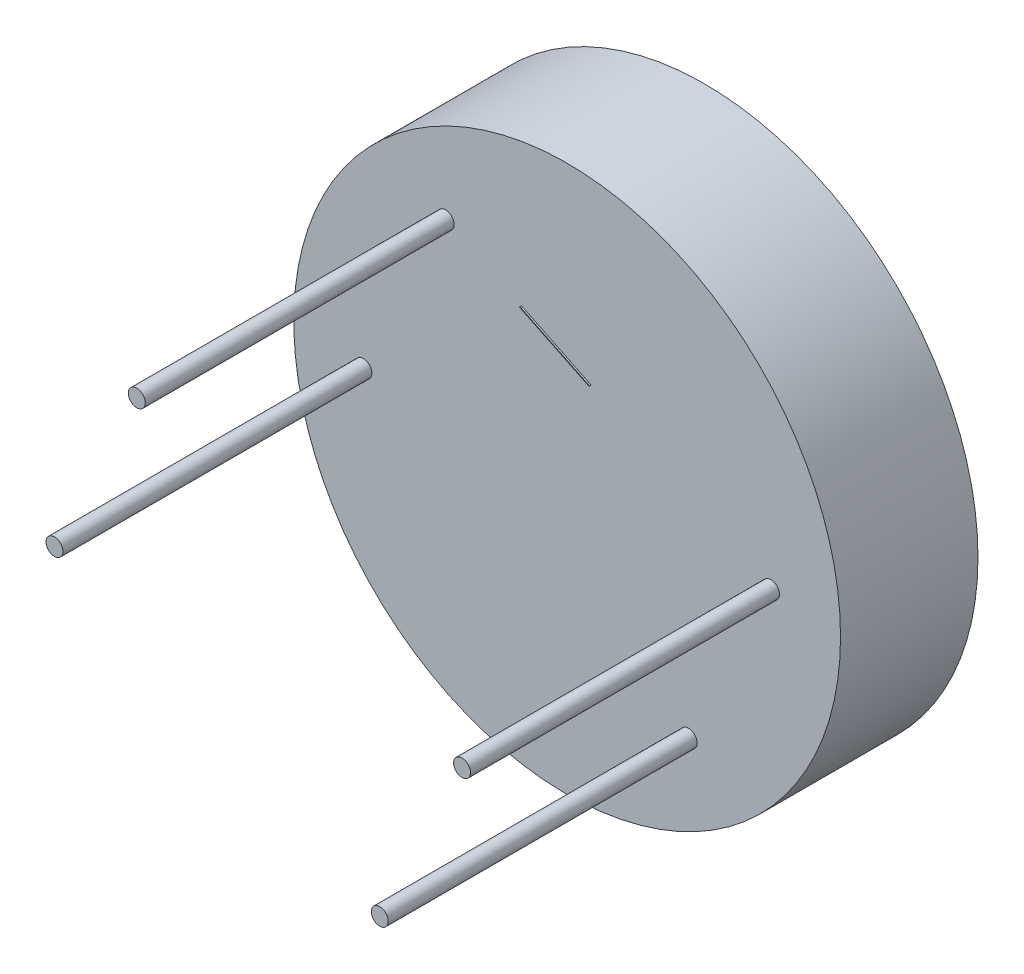
SolidWorks part; units mm, degrees
ref_plane "Plan de face" through (0, 0, 0) normal (0, 0, 1) x (1, 0, 0)
ref_plane "Plan de dessus" through (0, 0, 0) normal (0, 1, 0) x (1, 0, 0)
ref_plane "Plan de droite" through (0, 0, 0) normal (1, 0, 0) x (0, 0, -1)
sketch "Esquisse1" plane through (0, 0, 0) normal (0, 0, 1) x (1, 0, 0)
  circle A0 centre (0, 0) radius 177
  dimension "D1" = 354
extrude "Boss.-Extru.1" add sketch "Esquisse1" along normal blind 89
sketch "Esquisse2" plane through (0, 0, 89) normal (0, 0, 1) x (1, 0, 0)
  circle A0 centre (-131.9397, -3.9883) radius 5.5
  circle A1 centre (78.6481, -106.0117) radius 5.5
  circle A2 centre (131.9397, 3.9883) radius 5.5
  circle A3 centre (-78.6481, 106.0117) radius 5.5
  circle A4 centre (0, 0) radius 177 construction
  dimension "D1" = 11
  dimension "D2" = 11
  dimension "D3" = 11
  dimension "D4" = 11
  dimension "D6" = 132
  dimension "D7" = 132
  dimension "D8" = 132
  dimension "D5" = 132
  dimension "D9" = 234
  dimension "D10" = 110
  dimension "D11" = 234
  dimension "D12" = 110
extrude "Boss.-Extru.2" add sketch "Esquisse2" along normal blind 200
sketch "Esquisse3" [suppressed] plane through (0, 0, 89) normal (0, 0, 1) x (1, 0, 0)
  line L0 (-78.6481, 106.0117) -> (-131.9397, -3.9883) construction
  line L1 (-87.9507, 86.8101) -> (-120.4147, 19.8006)
  line L2 (-120.4147, 19.8006) -> (-119.9648, 19.5826)
  line L3 (-119.9648, 19.5826) -> (-87.5007, 86.5921)
  line L4 (-87.5007, 86.5921) -> (-87.9507, 86.8101)
  dimension "D1" = 0.5
extrude "Boss.-Extru.3" [suppressed] add sketch "Esquisse3" along normal blind 1
sketch "Esquisse4" plane through (0, 0, 89) normal (0, 0, 1) x (1, 0, 0)
  line L0 (-78.6481, 106.0117) -> (131.9397, 3.9883) construction
  line L1 (-29.6405, 82.269) -> (-29.8585, 81.8191)
  line L2 (-29.8585, 81.8191) -> (15.1389, 60.0192)
  line L3 (15.1389, 60.0192) -> (15.3569, 60.4692)
  line L4 (15.3569, 60.4692) -> (-29.6405, 82.269)
  dimension "D1" = 0.5
  dimension "D2" = 50
extrude "Boss.-Extru.4" add sketch "Esquisse4" along normal blind 1
